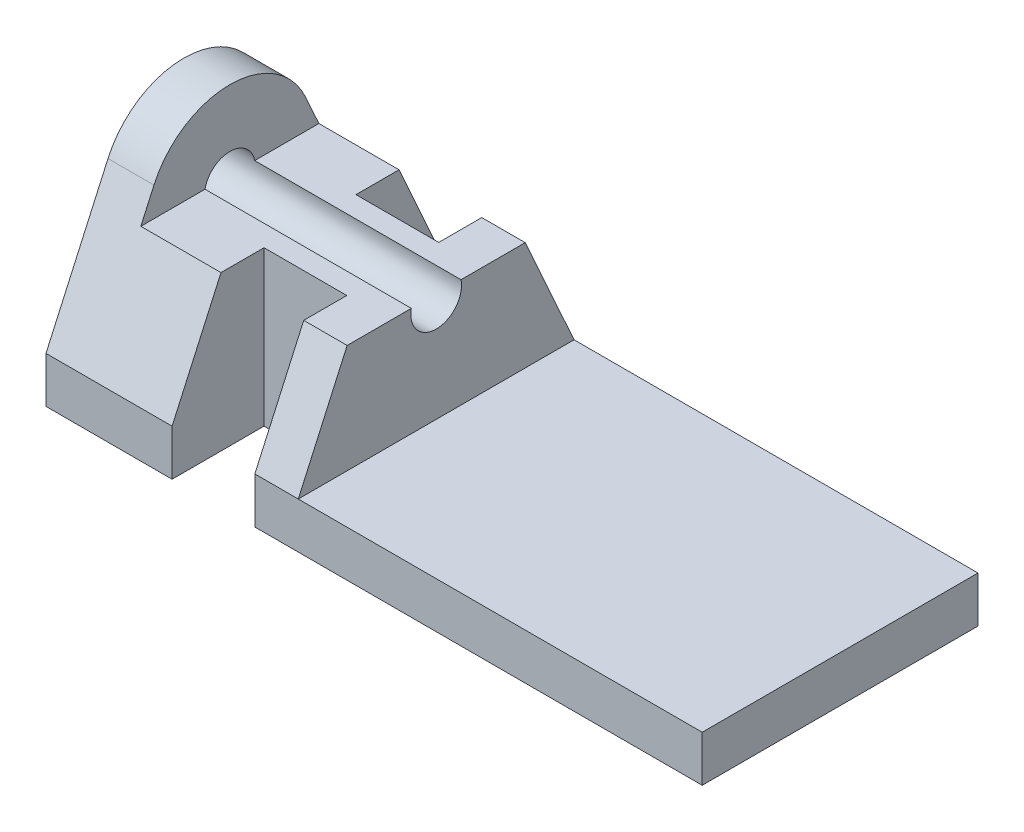
SolidWorks part; units mm, degrees
ref_plane "Front Plane" through (0, 0, 0) normal (0, 0, 1) x (1, 0, 0)
ref_plane "Top Plane" through (0, 0, 0) normal (0, 1, 0) x (1, 0, 0)
ref_plane "Right Plane" through (0, 0, 0) normal (1, 0, 0) x (0, 0, -1)
sketch "Sketch3" plane through (0, 0, 0) normal (1, 0, 0) x (0, -1, 0)
  point P0 (-14.3071, 0)
  dimension "D1" = 14.3071
sketch "Sketch5" plane through (0, 0, 0) normal (1, 0, 0) x (0, -1, 0)
  line L0 (6.35, 0) -> (-27.0071, 0) construction
  line L1 (6.35, -19.05) -> (-27.0071, -19.05)
  line L2 (6.35, -19.05) -> (6.35, 19.05)
  line L3 (6.35, 19.05) -> (-27.0071, 19.05)
  line L4 (-27.0071, -19.05) -> (-27.0071, 19.05)
  dimension "D1" = 12.7
  dimension "D2" = 38.1
  dimension "D3" = 6.35
extrude "Boss-Extrude2" add sketch "Sketch5" along normal blind 20.8 and the other way blind 69.85
sketch "Sketch6" plane through (0, 0, 19.05) normal (0, 0, 1) x (1, 0, 0)
  line L0 (-63.5, 27.0071) -> (-63.5, 0)
  line L1 (-63.5, 0) -> (20.8, 0)
  line L2 (-69.85, -6.35) -> (-69.85, 27.0071) construction
  line L4 (-69.85, -6.35) -> (20.8, -6.35)
  line L5 (20.8, -6.35) -> (20.8, 27.0071)
  line L6 (20.8, 27.0071) -> (-69.85, 27.0071)
  line L7 (-69.85, 27.0071) -> (-69.85, -6.35)
  line L9 (20.8, 0) -> (20.8, 27.0071)
  line L10 (20.8, 27.0071) -> (-63.5, 27.0071)
  dimension "D2" = 6.35
  dimension "D1" = 0
extrude "Cut-Extrude1" cut sketch "Sketch6" against normal through all
sketch "Sketch7" plane through (0, 0, 0) normal (1, 0, 0) x (0, 0, -1)
  circle A0 centre (0, 14.3071) radius 3.5
  dimension "D1" = 7
extrude "Cut-Extrude2" cut sketch "Sketch7" against normal through all and the other way through all
sketch "Sketch8" plane through (0, 0, 0) normal (1, 0, 0) x (0, 0, -1)
  line L0 (19.05, 0) -> (10.4869, 19.0268)
  line L1 (-19.05, 0) -> (-10.4869, 19.0268)
  line L4 (-19.05, 27.0071) -> (-19.05, 0)
  line L5 (-19.05, 0) -> (19.05, 0)
  line L6 (19.05, 0) -> (19.05, 27.0071)
  line L7 (19.05, 27.0071) -> (-19.05, 27.0071)
  line L8 (-19.05, 27.0071) -> (-19.05, 0)
  line L10 (19.05, 0) -> (19.05, 27.0071)
  line L11 (19.05, 27.0071) -> (-19.05, 27.0071)
  circle A2 centre (0, 14.3071) radius 11.5
  arc A3 (10.4869, 19.0268) -> (-10.4869, 19.0268) centre (0, 14.3071) ccw
  dimension "D1" = 0
  dimension "D2" = 8
extrude "Cut-Extrude3" cut sketch "Sketch8" against normal through all
sketch "Sketch9" plane through (0, 0, 0) normal (0, 1, 0) x (1, 0, 0)
  line L0 (-63.5, 19.05) -> (20.8, 19.05) construction
  line L1 (-63.5, -19.05) -> (-35, -19.05)
  line L2 (-63.5, -19.05) -> (-63.5, 19.05)
  line L3 (-63.5, 19.05) -> (-35, 19.05)
  line L4 (-35, -19.05) -> (-35, 19.05)
  dimension "D1" = 35
extrude "Boss-Extrude3" add sketch "Sketch9" along normal blind 15
sketch "Sketch10" plane through (0, 0, 0) normal (1, 0, 0) x (0, 0, -1)
  line L0 (-19.05, 0) -> (-10.4869, 19.0268) construction
  line L1 (10.4869, 19.0268) -> (19.05, 0) construction
  line L2 (-19.05, 0) -> (0, 42.328)
  line L3 (0, 42.328) -> (19.05, 0)
  line L4 (-19.05, 0) -> (-19.05, 42.328)
  line L5 (-19.05, 42.328) -> (0, 42.328)
  line L6 (0, 42.328) -> (19.05, 42.328)
  line L7 (19.05, 42.328) -> (19.05, 0)
extrude "Cut-Extrude4" cut sketch "Sketch10" against normal through all contours L7 L6 L3 | L5 L4 L2
sketch "Sketch11" plane through (0, 0, 0) normal (1, 0, 0) x (0, 0, -1)
  circle A0 centre (0, 14.3071) radius 3.5 construction
  circle A1 centre (0, 14.3071) radius 3.5
extrude "Cut-Extrude5" cut sketch "Sketch11" against normal through all
sketch "Sketch13" plane through (0, 0, 0) normal (0, 1, 0) x (1, 0, 0)
  line L0 (-41, -31.75) -> (-41, -6.35)
  line L1 (-41, -6.35) -> (-52.43, -6.35)
  line L2 (-52.43, -6.35) -> (-52.43, -31.75)
  line L3 (-52.43, -31.75) -> (-41, -31.75)
  line L4 (-23.9753, 0) -> (23.9753, 0) construction
  line L5 (-52.43, 31.75) -> (-41, 31.75)
  line L6 (-52.43, 6.35) -> (-52.43, 31.75)
  line L7 (-41, 6.35) -> (-52.43, 6.35)
  line L8 (-41, 31.75) -> (-41, 6.35)
  point P4 (-52.43, -19.05)
  dimension "D1" = 41
  dimension "D2" = 6.35
  dimension "D3" = 11.43
  dimension "D4" = 25.4
extrude "Cut-Extrude6" cut sketch "Sketch13" against normal through all and the other way through all
